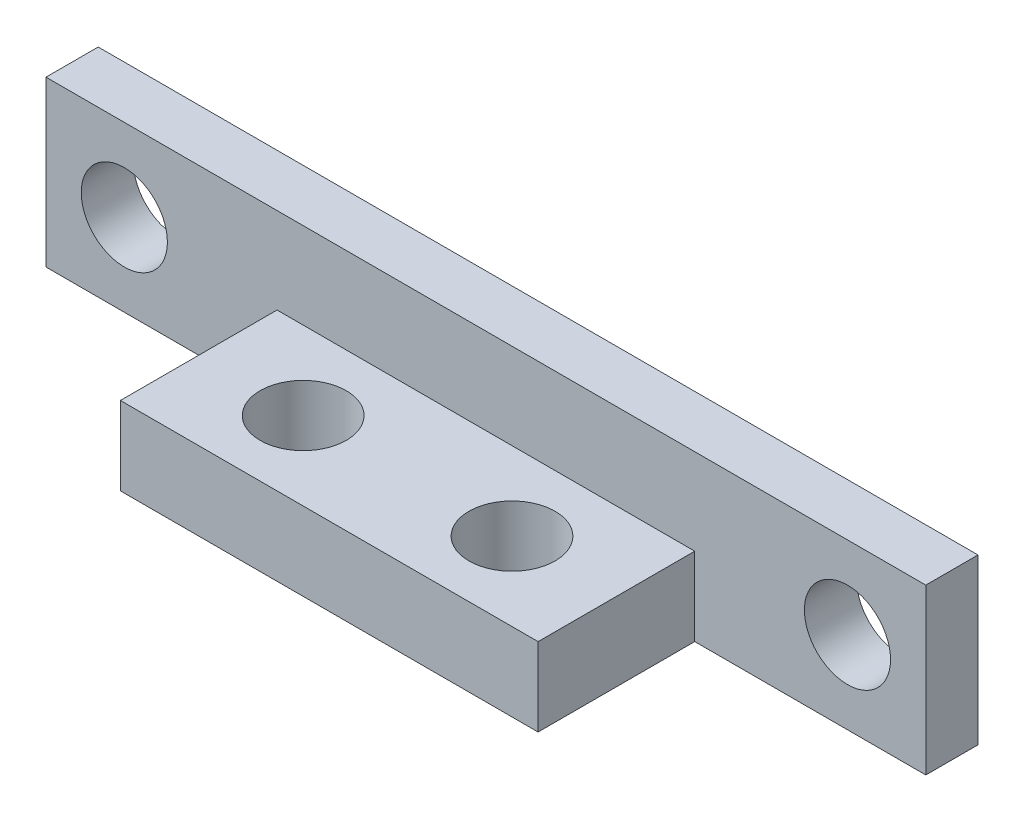
SolidWorks part; units mm, degrees
ref_plane "Front Plane" through (0, 0, 0) normal (0, 0, 1) x (1, 0, 0)
ref_plane "Top Plane" through (0, 0, 0) normal (0, 1, 0) x (1, 0, 0)
ref_plane "Right Plane" through (0, 0, 0) normal (1, 0, 0) x (0, 0, -1)
sketch "Sketch1" plane through (0, 0, 0) normal (0, 0, 1) x (1, 0, 0)
  line L1 (0, 0) -> (33.7, 0)
  line L2 (0, 0) -> (0, 6.3)
  line L3 (0, 6.3) -> (33.7, 6.3)
  line L4 (33.7, 0) -> (33.7, 6.3)
  circle A0 centre (3, 3.15) radius 1.65
  circle A1 centre (30.7, 3.15) radius 1.65
  dimension "D2" = 3.3
  dimension "D3" = 3.15
  dimension "D4" = 3
  dimension "D6" = 3.15
  dimension "D7" = 27.7
  dimension "D1" = 6.3
  dimension "D5" = 3
extrude "Boss-Extrude1" add sketch "Sketch1" along normal blind 2
sketch "Sketch2" plane through (0, 0, 2) normal (0, 0, 1) x (1, 0, 0)
  line L0 (0, 0) -> (33.7, 0) construction
  line L1 (8.85, 0) -> (24.85, 0)
  line L2 (8.85, 0) -> (8.85, 3)
  line L3 (8.85, 3) -> (24.85, 3)
  line L4 (24.85, 0) -> (24.85, 3)
  line L5 (8.85, 0) -> (0, 0) construction
  line L6 (24.85, 0) -> (33.7, 0) construction
  dimension "D1" = 3
  dimension "D2" = 16
extrude "Boss-Extrude2" add sketch "Sketch2" along normal blind 6
sketch "Sketch3" plane through (0, 3, 0) normal (0, 1, 0) x (1, 0, 0)
  line L0 (12.85, -5) -> (8.85, -5) construction
  line L1 (8.85, -8) -> (8.85, -2) construction
  line L2 (20.85, -5) -> (24.85, -5) construction
  line L3 (24.85, -8) -> (24.85, -2) construction
  line L4 (24.85, -8) -> (8.85, -8) construction
  circle A0 centre (12.85, -5) radius 1.65
  circle A1 centre (20.85, -5) radius 1.65
  dimension "D1" = 3.3
  dimension "D2" = 3.3
  dimension "D3" = 8
  dimension "D4" = 3
  dimension "D5" = 3
extrude "Cut-Extrude1" cut sketch "Sketch3" against normal blind 6
